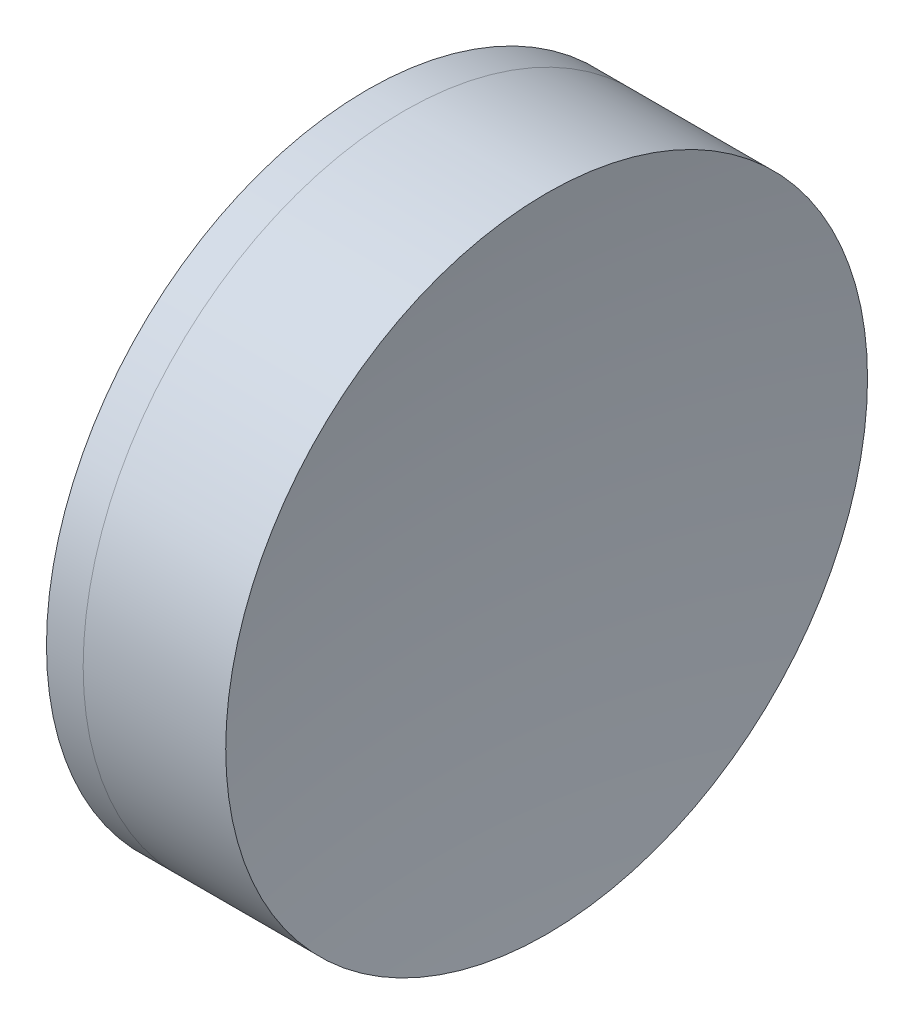
SolidWorks part; units mm, degrees
ref_plane "前视基准面" through (0, 0, 0) normal (0, 0, 1) x (1, 0, 0)
ref_plane "上视基准面" through (0, 0, 0) normal (0, 1, 0) x (1, 0, 0)
ref_plane "右视基准面" through (0, 0, 0) normal (1, 0, 0) x (0, 0, -1)
sketch "草图1" plane through (0, 0, 0) normal (0, 1, 0) x (1, 0, 0)
  line L0 (-0.8161, 0) -> (45.8933, 0) construction
  line L1 (37.4913, -12.7) -> (38.9435, -12.7)
  line L2 (37.4913, 12.7) -> (38.9435, 12.7)
  arc A0 (38.9435, -12.7) -> (38.9435, 12.7) centre (12.4502, 0) ccw
  arc A1 (37.4913, 12.7) -> (37.4913, -12.7) centre (60.5902, 0) ccw
  point P10 (34.2302, 0)
  point P11 (41.8302, 0)
  dimension "D3" = 26.36
  dimension "D4" = 29.38
  dimension "D1" = 12.7
  dimension "D2" = 12.7
  dimension "D5" = 7.6
revolve "旋转1" add sketch "草图1" angle 360 about L0
sketch "草图2" plane through (0, 0, 0) normal (0, 1, 0) x (1, 0, 0)
  line L0 (-0.5519, 0) -> (45.4982, 0) construction
  line L2 (38.9435, 12.7) -> (44.5853, 12.7)
  line L3 (38.9435, -12.7) -> (44.5853, -12.7)
  arc A0 (44.5853, 12.7) -> (44.5853, -12.7) centre (128.5502, 0) ccw
  arc A1 (38.9435, -12.7) -> (38.9435, 12.7) centre (12.4502, 0) ccw construction
  arc A2 (38.9435, -12.7) -> (38.9435, 12.7) centre (12.4502, 0) ccw
  point P4 (41.8302, 0)
  point P8 (43.6302, 0)
  dimension "D1" = 84.92
  dimension "D2" = 1.8
revolve "旋转2" add sketch "草图2" angle 360 about L0
